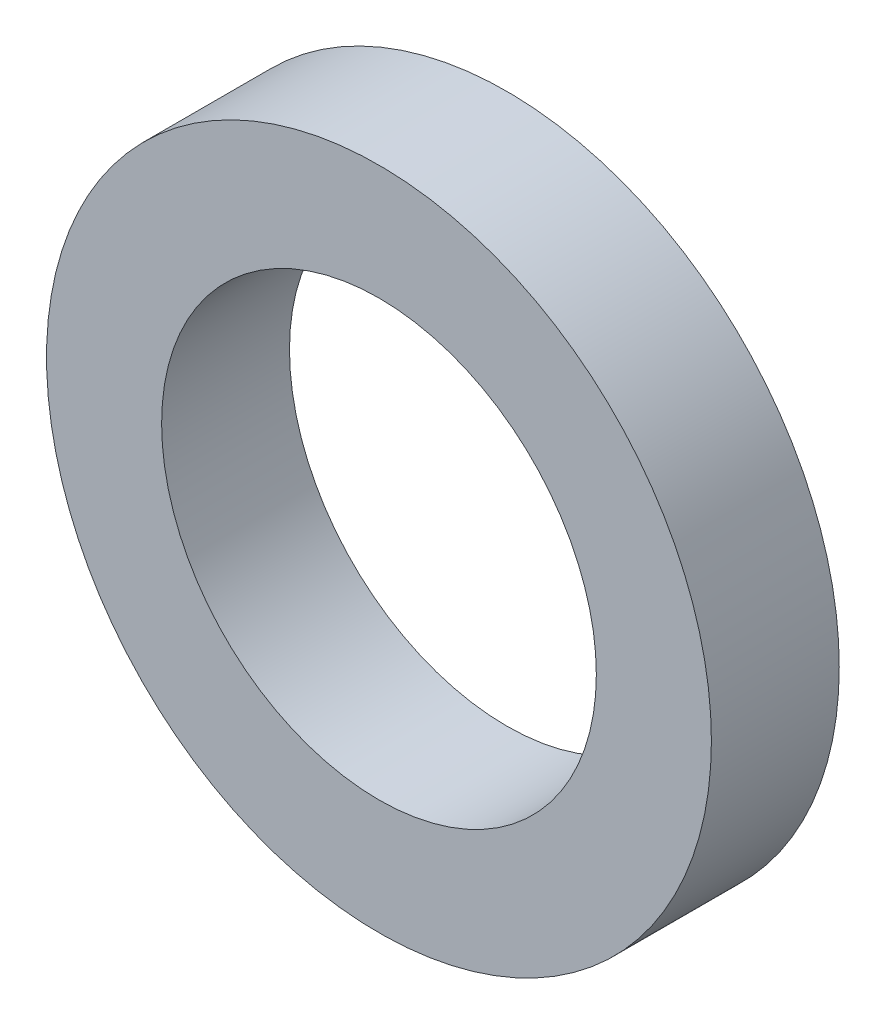
SolidWorks part; units mm, degrees
ref_plane "Front Plane" through (0, 0, 0) normal (0, 0, 1) x (1, 0, 0)
ref_plane "Top Plane" through (0, 0, 0) normal (0, 1, 0) x (1, 0, 0)
ref_plane "Right Plane" through (0, 0, 0) normal (1, 0, 0) x (0, 0, -1)
sketch "Sketch1" plane through (0, 0, 0) normal (0, 0, 1) x (1, 0, 0)
  circle A0 centre (0, 0) radius 13
  dimension "D1" = 26
extrude "Boss-Extrude1" add sketch "Sketch1" along normal blind 5
sketch "Sketch2" plane through (0, 0, 5) normal (0, 0, 1) x (1, 0, 0)
  circle A0 centre (0, 0) radius 8.5
  dimension "D1" = 17
extrude "Cut-Extrude1" cut sketch "Sketch2" against normal blind 5
